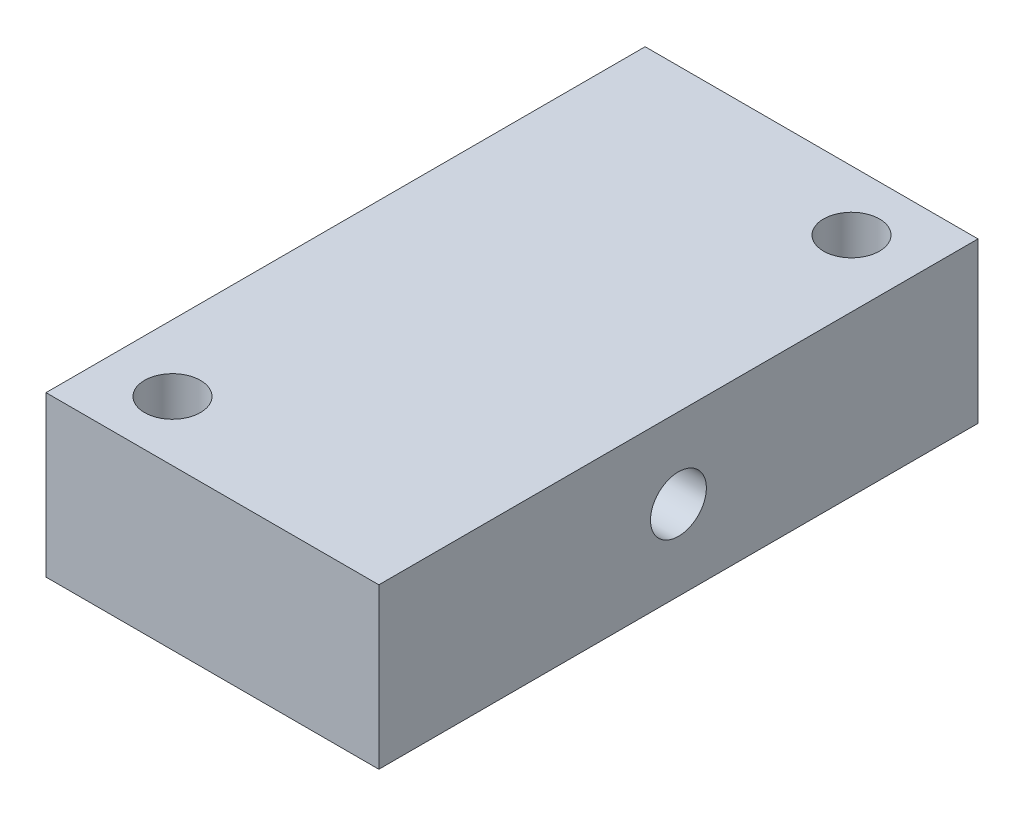
SolidWorks part; units mm, degrees
ref_plane "Front Plane" through (0, 0, 0) normal (0, 0, 1) x (1, 0, 0)
ref_plane "Top Plane" through (0, 0, 0) normal (0, 1, 0) x (1, 0, 0)
ref_plane "Right Plane" through (0, 0, 0) normal (1, 0, 0) x (0, 0, -1)
sketch "Sketch1" plane through (0, 0, 0) normal (0, 1, 0) x (1, 0, 0)
  line L1 (-12.5, -22.5) -> (12.5, -22.5)
  line L2 (-12.5, -22.5) -> (-12.5, 22.5)
  line L3 (-12.5, 22.5) -> (12.5, 22.5)
  line L4 (12.5, -22.5) -> (12.5, 22.5)
  line L5 (-12.5, -22.5) -> (12.5, 22.5) construction
  line L6 (-12.5, 22.5) -> (12.5, -22.5) construction
  point P0 (0, 0)
  dimension "D1" = 25
  dimension "D2" = 45
extrude "Boss-Extrude1" add sketch "Sketch1" along normal blind 12
hole_wizard "M5 Tapped Hole1" positions "Sketch2" profile "Sketch3" tap size "M5" standard "DIN" end condition through all
sketch "Sketch2" plane through (0, 12, 0) normal (0, 1, 0) x (1, 0, 0)
  point P0 (7.5, 18)
  point P2 (-7.5, -18)
  dimension "D1" = 7.5
  dimension "D2" = 18
  dimension "D3" = 18
  dimension "D4" = 7.5
sketch "Sketch3" plane through (7.5, 12, -18) normal (1, 0, 0) x (0, 0, 1)
  line L0 (0, 0) -> (0, 12)
  line L1 (0, 12) -> (2.1, 12)
  line L2 (2.1, 12) -> (2.1, 0)
  line L5 (2.1, 0) -> (0, 0)
  line L11 (0, -6.35) -> (0, 107.95) construction
  dimension "Thru Tap Drill Dia." = 4.2
  dimension "Thru Tap Drill Depth" = 12
cosmetic thread "Hole Thread1" parameters "D2"=5
cosmetic thread "Hole Thread2" parameters "D2"=5
hole_wizard "M5 Tapped Hole2" positions "Sketch4" profile "Sketch5" tap size "M5" standard "DIN" end condition through all
sketch "Sketch4" plane through (12.5, 0, 0) normal (1, 0, 0) x (0, 0, -1)
  line L0 (-22.5, 12) -> (22.5, 12) construction
  point P0 (0, 6)
  point P5 (0, 12)
  dimension "D1" = 6
sketch "Sketch5" plane through (12.5, 6, 0) normal (0, 1, 0) x (0, 0, -1)
  line L0 (0, 0) -> (0, 25)
  line L1 (0, 25) -> (2.1, 25)
  line L2 (2.1, 25) -> (2.1, 0)
  line L5 (2.1, 0) -> (0, 0)
  line L11 (0, -6.35) -> (0, 107.95) construction
  dimension "Thru Tap Drill Dia." = 4.2
  dimension "Thru Tap Drill Depth" = 25
cosmetic thread "Hole Thread3" parameters "D2"=5
